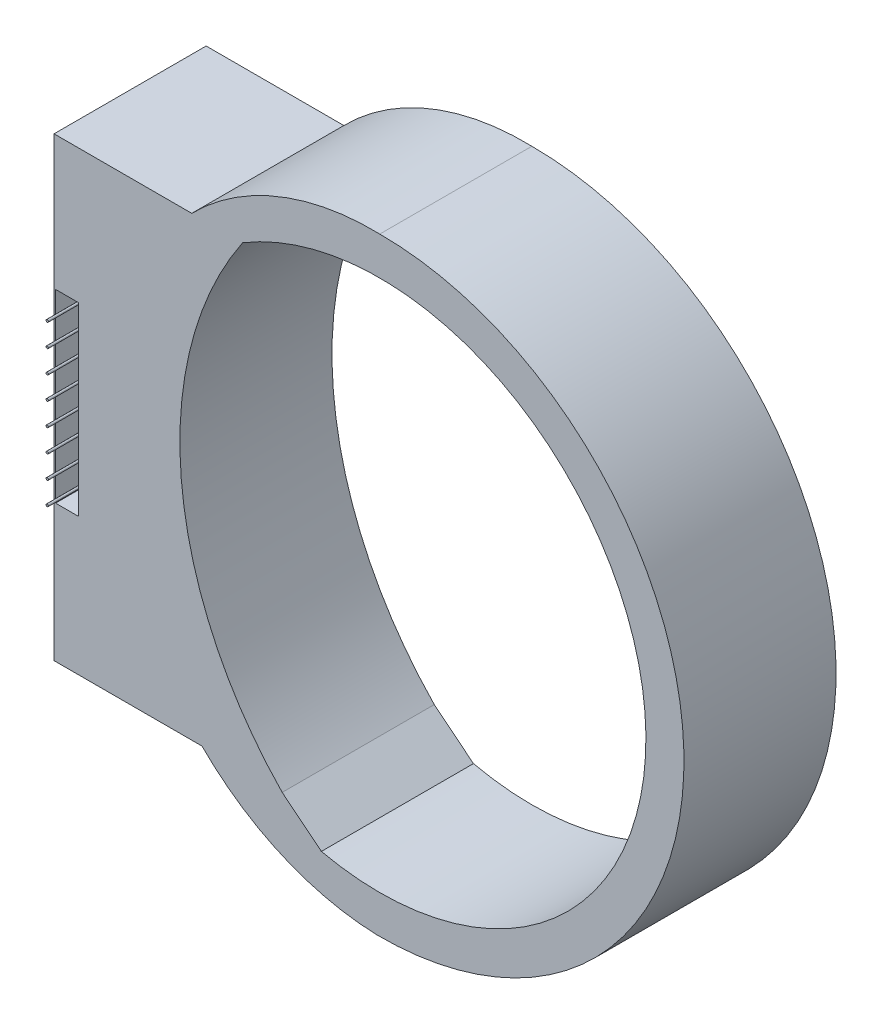
SolidWorks part; units mm, degrees
ref_plane "Front Plane" through (0, 0, 0) normal (1, 0, 0) x (0, 1, 0)
ref_plane "Top Plane" through (0, 0, 0) normal (0, 0, 1) x (0, 1, 0)
ref_plane "Right Plane" through (0, 0, 0) normal (0, 1, 0) x (-1, 0, 0)
sketch "Sketch1" plane through (0, 0, 0) normal (0, 0, 1) x (0, 1, 0)
  line L1 (38.1, 31.3961) -> (38.1, 54.397)
  line L2 (38.1, 54.397) -> (-38.1, 54.397)
  line L3 (-38.1, 54.397) -> (-38.1, 29.6869)
  line L6 (-38.1, 16.297) -> (-43.3663, 9.7554)
  line L7 (-43.3663, 9.7554) -> (-38.1, 16.297)
  arc A1 (-50.7973, 0.5249) -> (50.8, 0) centre (0, 0) ccw
  arc A2 (-43.3663, 9.7554) -> (38.1, 22.8953) centre (0, 0) ccw
  arc A3 (-50.7973, 0.5249) -> (-38.1, 29.6869) centre (-7.592, -0.9416) cw
  arc A4 (50.8, 0) -> (38.1, 31.3961) centre (8.4315, 1.1282) ccw
  arc A5 (-38.1, 16.297) -> (38.1, 22.8953) centre (4.0482, -27.1543) cw
  point P6 (0, 54.397)
  dimension "D1" = 88.9
  dimension "D2" = 0
  dimension "D5" = 50.8
  dimension "D3" = 76.2
  dimension "D4" = 38.1
extrude "Boss-Extrude1" add sketch "Sketch1" along normal blind 25.4
sketch "Sketch2" plane through (0, 0, 25.4) normal (0, 0, 1) x (1, 0, 0)
  line L0 (-54.397, 38.1) -> (-54.397, -38.1) construction
  line L1 (-54.143, 15.7258) -> (-50.333, 15.7258)
  line L2 (-54.143, 15.7258) -> (-54.143, -15.1881)
  line L3 (-54.143, -15.1881) -> (-50.333, -15.1881)
  line L4 (-50.333, 15.7258) -> (-50.333, -15.1881)
  point P4 (-54.397, 0)
  point P7 (-54.143, 0.2688)
  dimension "D1" = 3.81
  dimension "D2" = 15.1881
  dimension "D3" = 0.254
extrude "Cut-Extrude1" cut sketch "Sketch2" against normal blind 24.638
sketch "Sketch3" plane through (0, 0, 0.762) normal (0, 0, 1) x (1, 0, 0)
  circle A0 centre (-52.238, -12.905) radius 0.1905
  circle A1 centre (-52.238, -9.095) radius 0.1905
  circle A2 centre (-52.238, -5.285) radius 0.1905
  circle A3 centre (-52.238, -1.475) radius 0.1905
  circle A4 centre (-52.238, 2.335) radius 0.1905
  circle A5 centre (-52.238, 6.145) radius 0.1905
  circle A6 centre (-52.238, 9.955) radius 0.1905
  circle A7 centre (-52.238, 13.765) radius 0.1905
  dimension "D1" = 0.381
  dimension "D2" = 8
extrude "Boss-Extrude2" add sketch "Sketch3" along normal blind 27.94
sketch "Sketch4" plane through (0, 0, 28.702) normal (0, 0, 1) x (1, 0, 0)
  circle A1 centre (-52.238, -12.905) radius 0.1905
  circle A2 centre (-52.238, -12.905) radius 0.1905
  ellipse E1 centre (11.3299, -46.0302) end of major axis (11.4116, -45.933) minor radius 0.1085
  ellipse E2 centre (11.3299, -46.0302) end of major axis (11.4116, -45.933) minor radius 0.1085
  dimension "D1" = 0
  dimension "D2" = 0
